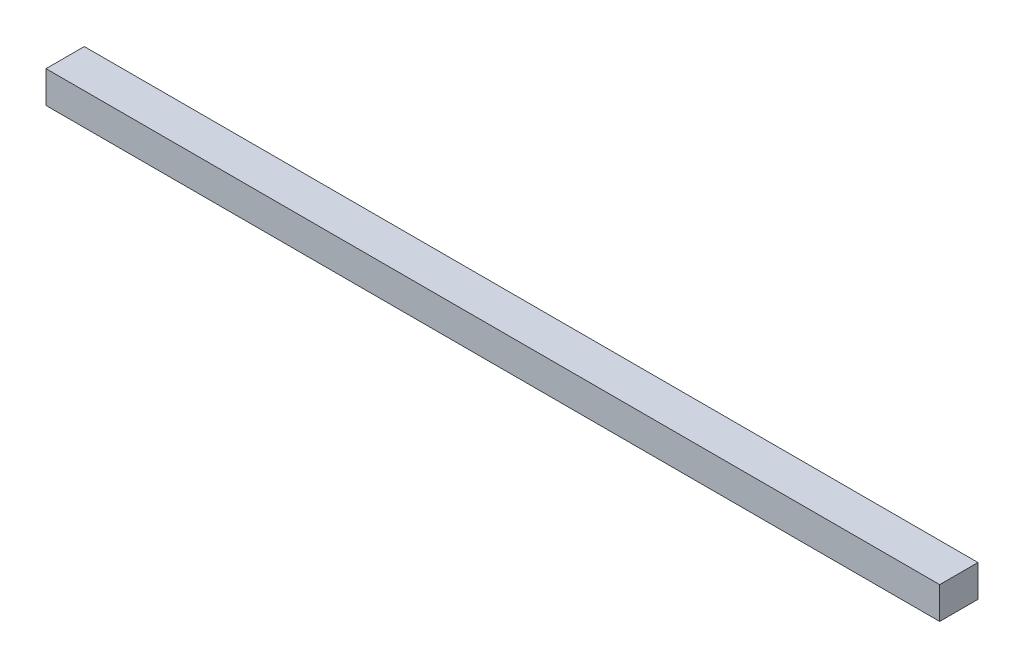
SolidWorks part; units mm, degrees
ref_plane "Front Plane" through (0, 0, 0) normal (0, 0, 1) x (1, 0, 0)
ref_plane "Top Plane" through (0, 0, 0) normal (0, 1, 0) x (1, 0, 0)
ref_plane "Right Plane" through (0, 0, 0) normal (1, 0, 0) x (0, 0, -1)
sketch "Sketch1" plane through (0, 0, 0) normal (1, 0, 0) x (0, 0, -1)
  line L1 (0, 0) -> (30, 0)
  line L2 (0, 0) -> (0, 25)
  line L3 (0, 25) -> (30, 25)
  line L4 (30, 0) -> (30, 25)
  dimension "D1" = 30
  dimension "D2" = 25
extrude "Boss-Extrude1" add sketch "Sketch1" along normal blind 700
